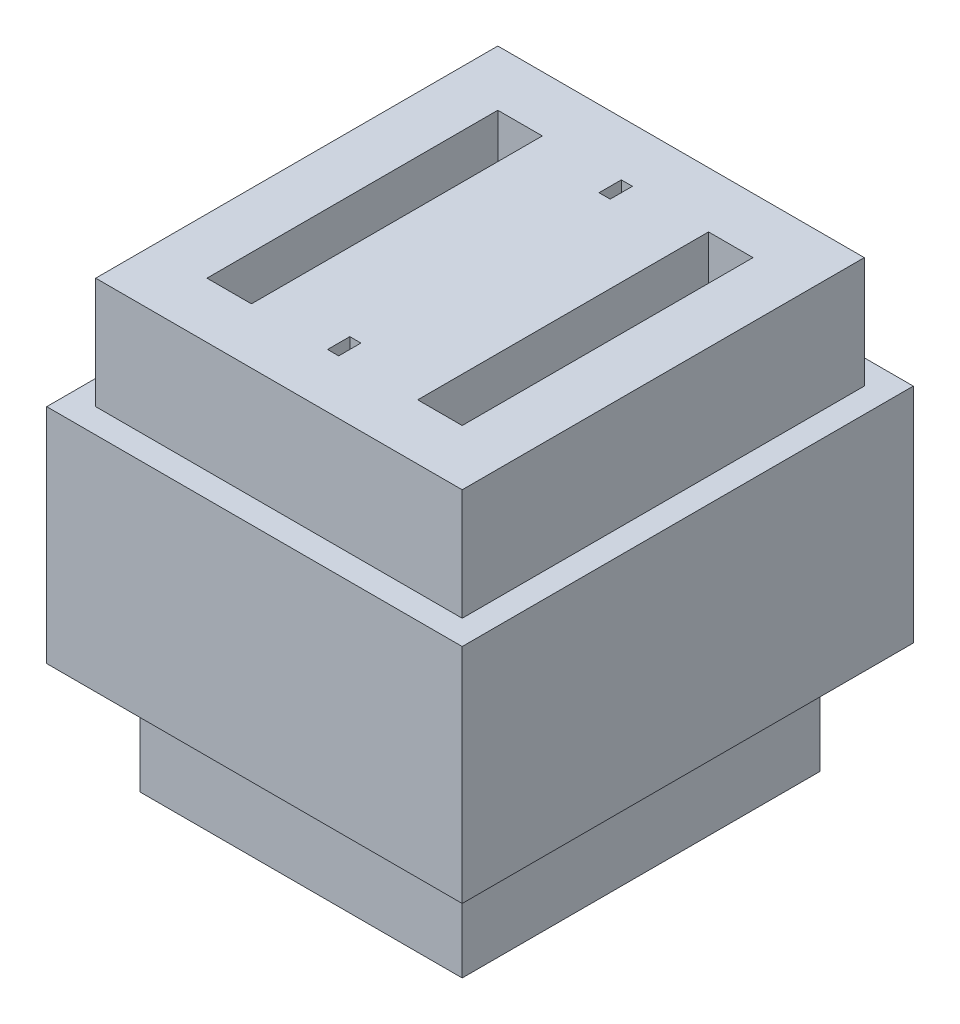
SolidWorks part; units mm, degrees
ref_plane "Front Plane" through (0, 0, 0) normal (0, 0, 1) x (1, 0, 0)
ref_plane "Top Plane" through (0, 0, 0) normal (0, 1, 0) x (1, 0, 0)
ref_plane "Right Plane" through (0, 0, 0) normal (1, 0, 0) x (0, 0, -1)
sketch "Sketch1" plane through (0, 0, 0) normal (0, 1, 0) x (1, 0, 0)
  line L0 (-9.335, 10.135) -> (9.335, -10.135) construction
  line L2 (-9.335, 10.135) -> (9.335, 10.135)
  line L3 (-9.335, 10.135) -> (-9.335, -10.135)
  line L4 (-9.335, -10.135) -> (9.335, -10.135)
  line L5 (9.335, 10.135) -> (9.335, -10.135)
  point P2 (0, 0)
  dimension "D1" = 18.67
  dimension "D2" = 20.27
extrude "Boss-Extrude1" add sketch "Sketch1" along normal mid plane 20
sketch "Sketch2" plane through (0, 10, 0) normal (0, 1, 0) x (1, 0, 0)
  line L4 (-9.335, 10.135) -> (-9.335, -10.135) construction
  line L5 (-9.335, -10.135) -> (9.335, -10.135) construction
  line L6 (9.335, -10.135) -> (9.335, 10.135) construction
  line L7 (9.335, 10.135) -> (-9.335, 10.135) construction
  line L8 (-8.235, 9.035) -> (-8.235, -9.035)
  line L9 (-8.235, -9.035) -> (8.235, -9.035)
  line L10 (8.235, -9.035) -> (8.235, 9.035)
  line L11 (8.235, 9.035) -> (-8.235, 9.035)
  line L12 (-8.235, 9.035) -> (-8.235, -9.035)
  line L13 (-8.235, -9.035) -> (8.235, -9.035)
  line L14 (8.235, -9.035) -> (8.235, 9.035)
  line L15 (8.235, 9.035) -> (-8.235, 9.035)
  line L16 (-9.335, 10.135) -> (-9.335, -10.135)
  line L17 (-9.335, -10.135) -> (9.335, -10.135)
  line L18 (9.335, -10.135) -> (9.335, 10.135)
  line L19 (9.335, 10.135) -> (-9.335, 10.135)
  dimension "D1" = 1.1
extrude "Cut-Extrude1" cut sketch "Sketch2" against normal blind 5
sketch "Sketch7" plane through (0, -10, 0) normal (0, -1, 0) x (1, 0, 0)
  line L6 (-9.335, 10.135) -> (-9.335, -10.135) construction
  line L7 (-9.335, -10.135) -> (9.335, -10.135) construction
  line L8 (9.335, -10.135) -> (9.335, 10.135) construction
  line L9 (-7.235, 8.035) -> (-7.235, -8.035)
  line L10 (-7.235, -8.035) -> (7.235, -8.035)
  line L11 (7.235, -8.035) -> (7.235, 8.035)
  line L12 (7.235, 8.035) -> (-7.235, 8.035)
  line L13 (-7.235, 8.035) -> (-7.235, -8.035)
  line L14 (-7.235, -8.035) -> (7.235, -8.035)
  line L15 (7.235, -8.035) -> (7.235, 8.035)
  line L16 (7.235, 8.035) -> (-7.235, 8.035)
  line L17 (9.335, 10.135) -> (-9.335, 10.135) construction
  line L18 (-9.335, 10.135) -> (-9.335, -10.135)
  line L19 (-9.335, -10.135) -> (9.335, -10.135)
  line L20 (9.335, -10.135) -> (9.335, 10.135)
  line L21 (9.335, 10.135) -> (-9.335, 10.135)
  dimension "D1" = 2.1
extrude "Cut-Extrude5" cut sketch "Sketch7" against normal blind 5
sketch "Sketch3" plane through (0, -10, 0) normal (0, -1, 0) x (1, 0, 0)
  line L9 (5.235, 6.035) -> (-5.235, 6.035)
  line L10 (5.235, 6.035) -> (-5.235, 6.035)
  line L11 (-5.235, 6.035) -> (-5.235, -6.035)
  line L12 (-5.235, 6.035) -> (-5.235, -6.035)
  line L13 (-5.235, -6.035) -> (5.235, -6.035)
  line L14 (-5.235, -6.035) -> (5.235, -6.035)
  line L15 (5.235, -6.035) -> (5.235, 6.035)
  line L16 (5.235, -6.035) -> (5.235, 6.035)
  dimension "D1" = 2
extrude "Cut-Extrude2" cut sketch "Sketch3" against normal offset from surface (16 mm away) 4 up to face at (0, 10, 0)
sketch "Sketch4" plane through (0, 10, 0) normal (0, 1, 0) x (1, 0, 0)
  line L0 (0, 0) -> (4.1586, 0) construction
  line L2 (-5.735, -6.535) -> (-3.735, -6.535)
  line L3 (-5.735, -6.535) -> (-5.735, 6.535)
  line L4 (-5.735, 6.535) -> (-3.735, 6.535)
  line L5 (-3.735, -6.535) -> (-3.735, 6.535)
  line L7 (0, 0) -> (0, 6.7226) construction
  line L8 (5.735, -6.535) -> (3.735, -6.535)
  line L9 (3.735, -6.535) -> (3.735, 6.535)
  line L10 (5.735, 6.535) -> (3.735, 6.535)
  line L11 (5.735, -6.535) -> (5.735, 6.535)
  line L15 (8.235, -9.035) -> (8.235, 9.035) construction
  line L16 (-8.235, -9.035) -> (8.235, -9.035) construction
  point P7 (-3.735, 0)
  dimension "D1" = 2
  dimension "D2" = 2.5
  dimension "D3" = 2.5
extrude "Cut-Extrude3" cut sketch "Sketch4" against normal up to surface (10 mm away)
sketch "Sketch6" plane through (0, 6, 0) normal (0, -1, 0) x (1, 0, 0)
  line L1 (-1.75, -6.035) -> (1.75, -6.035)
  line L2 (-1.75, -6.035) -> (-1.75, 6.035)
  line L3 (-1.75, 6.035) -> (1.75, 6.035)
  line L4 (1.75, -6.035) -> (1.75, 6.035)
  line L6 (-1.75, -6.035) -> (1.75, 6.035) construction
  line L7 (3.735, 6.035) -> (-3.735, 6.035) construction
  point P8 (0, 0)
  dimension "D1" = 3.5
extrude "Boss-Extrude2" add sketch "Sketch6" along normal blind 5
sketch "Sketch5" plane through (0, 10, 0) normal (0, 1, 0) x (1, 0, 0)
  line L0 (0, 0) -> (-1.3876, 0) construction
  line L1 (0, 0) -> (0, 1.4388) construction
  line L2 (-0.25, -6.1) -> (-0.4283, -6.1) construction
  line L3 (-0.25, -6.6) -> (0.25, -6.6)
  line L4 (-0.25, -6.6) -> (-0.25, -5.6)
  line L5 (-0.25, -5.6) -> (0.25, -5.6)
  line L6 (0.25, -6.6) -> (0.25, -5.6)
  line L7 (0.25, 6.6) -> (0.25, 5.6)
  line L8 (-0.25, 5.6) -> (0.25, 5.6)
  line L9 (-0.25, 6.6) -> (-0.25, 5.6)
  line L10 (-0.25, 6.6) -> (0.25, 6.6)
  point P8 (0, -5.6)
  dimension "D1" = 6.1
  dimension "D2" = 0.5
  dimension "D3" = 1
extrude "Cut-Extrude4" cut sketch "Sketch5" against normal blind 7
